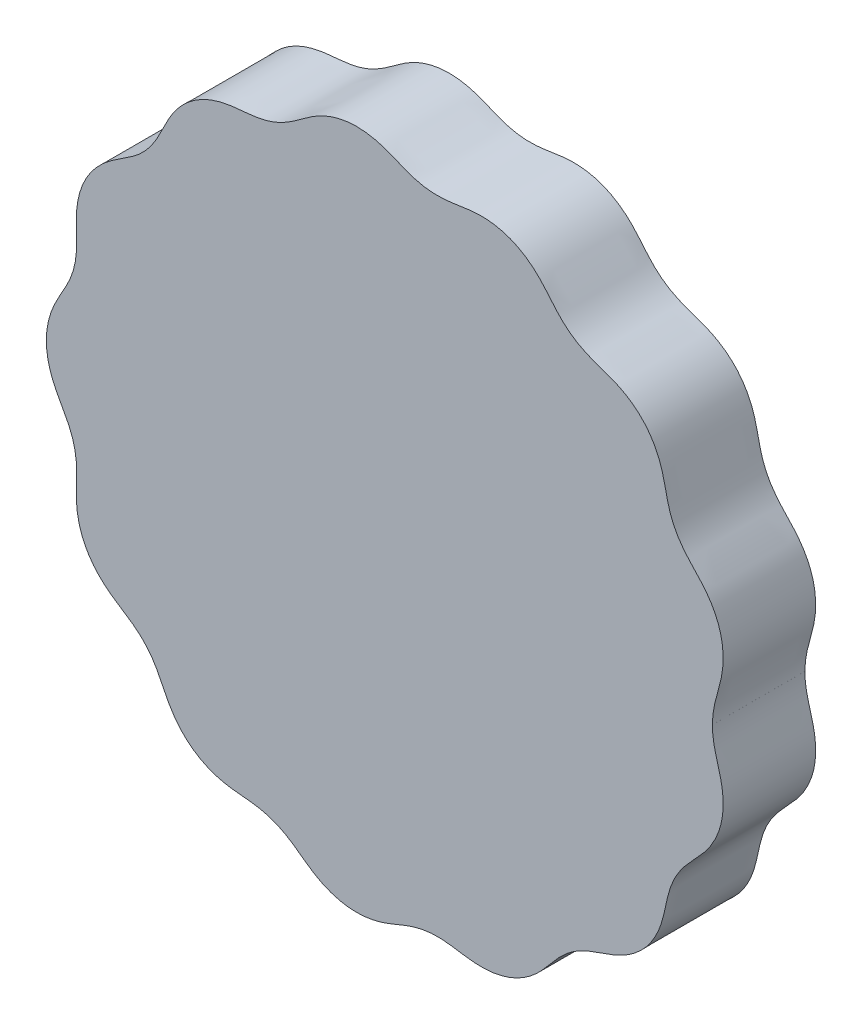
SolidWorks part; units mm, degrees
ref_plane "Front Plane" through (0, 0, 0) normal (0, 0, 1) x (1, 0, 0)
ref_plane "Top Plane" through (0, 0, 0) normal (0, 1, 0) x (1, 0, 0)
ref_plane "Right Plane" through (0, 0, 0) normal (1, 0, 0) x (0, 0, -1)
sketch "Sketch1" plane through (0, 0, 0) normal (0, 0, 1) x (1, 0, 0)
  spline S0 degree 4 poles (29.7584, 20.3385) (29.7891, 20.21) (29.8482, 19.9526) (29.9598, 19.4358) (30.1239, 18.6606) (30.3526, 17.7631) (30.7964, 16.5535) (31.4244, 15.4416) (32.2108, 14.4638) (33.1915, 13.4281) (34.1349, 12.4283) (35.0241, 11.2132) (35.7198, 9.7379) (36.1228, 8.1778) (36.2154, 6.7983) (36.1087, 5.5837) (35.9167, 4.6243) (35.7472, 3.9584) (35.5841, 3.3729) (35.4416, 2.864) (35.3243, 2.4166) (35.2341, 2.0306) (35.1681, 1.7068) (35.1214, 1.4469) (35.0816, 1.1852) (35.0491, 0.9241) (35.0274, 0.6907) (35.0151, 0.515) (35.0085, 0.3814) (35.0032, 0.2408) (34.9995, 0.0558) (34.9993, -0.0463) (35.0036, -0.2609) (35.011, -0.4439) (35.0217, -0.6152) (35.0388, -0.8202) (35.0646, -1.0542) (35.1044, -1.3447) (35.1634, -1.6922) (35.2469, -2.0945) (35.3584, -2.5508) (35.4807, -3.0042) (35.6346, -3.553) (35.8127, -4.1993) (35.9906, -4.9498) (36.1279, -5.8113) (36.1828, -6.6338) (36.163, -7.4097) (36.0619, -8.3015) (35.8756, -9.1315) (35.6003, -9.9363) (35.2413, -10.706) (34.9069, -11.2975) (34.4713, -11.9491) (33.919, -12.6455) (33.2464, -13.3753) (32.4862, -14.1654) (31.7296, -15.0492) (31.0461, -16.0739) (30.5313, -17.1947) (30.1828, -18.3744) (29.944, -19.5117) (29.7144, -20.5842) (29.2958, -22.0281) (28.4622, -23.7586) (27.0395, -25.4117) (25.2208, -26.5522) (23.6326, -27.1562) (22.3082, -27.5963) (21.1226, -28.0489) (19.9984, -28.666) (18.9904, -29.4694) (18.1793, -30.3103) (17.5068, -31.117) (16.775, -32.0038) (15.9108, -32.911) (14.604, -33.9568) (12.974, -34.7587) (11.1723, -35.1688) (9.4524, -35.1689) (8.1807, -35.0073) (7.0608, -34.8246) (6.0778, -34.7001) (4.9253, -34.6549) (3.6117, -34.7857) (2.349, -35.145) (1.1515, -35.6432) (0.1111, -36.0773) (-0.7914, -36.3968) (-2.1459, -36.7469) (-3.9895, -36.8999) (-5.8676, -36.5696) (-7.6084, -35.7603) (-8.8563, -34.9233) (-9.733, -34.2648) (-10.6766, -33.5857) (-11.7416, -32.9684) (-12.8897, -32.517) (-14.0912, -32.248) (-15.2466, -32.1165) (-16.3395, -32.0314) (-17.4939, -31.8907) (-18.6927, -31.6153) (-20.2224, -31.0274) (-21.7615, -30.0159) (-23.1071, -28.5705) (-24.107, -26.7907) (-24.8246, -25.168) (-25.6288, -23.8316) (-26.5069, -22.8288) (-27.3779, -22.0818) (-28.1653, -21.5233) (-29.1173, -20.9169) (-30.1989, -20.207) (-31.2694, -19.3076) (-32.2317, -18.16) (-32.9494, -16.9232) (-33.4333, -15.6485) (-33.6955, -14.3778) (-33.7784, -13.1508) (-33.7526, -11.9888) (-33.7086, -10.893) (-33.7328, -9.7296) (-33.9076, -8.5101) (-34.2723, -7.3318) (-34.7987, -6.2202) (-35.3756, -5.2116) (-35.913, -4.2559) (-36.5515, -2.8948) (-37.0651, -1.0442) (-37.082, 0.8932) (-36.604, 2.7435) (-35.9923, 4.1013) (-35.4727, 5.0451) (-34.8935, 6.0468) (-34.342, 7.1566) (-33.946, 8.3403) (-33.7454, 9.5758) (-33.7062, 10.7488) (-33.746, 11.8447) (-33.7797, 13.0063) (-33.7137, 14.234) (-33.4725, 15.5088) (-33.0106, 16.7916) (-32.323, 18.0254) (-31.4056, 19.1641) (-30.3765, 20.071) (-29.3206, 20.7894) (-28.3591, 21.3964) (-27.534, 21.9617) (-26.6421, 22.6971) (-25.7533, 23.6668) (-25.0522, 24.7709) (-24.489, 25.9341) (-23.9968, 26.9508) (-23.5268, 27.7958) (-22.7368, 28.9589) (-21.4481, 30.2928) (-19.8158, 31.2833) (-17.9732, 31.822) (-16.4836, 32.0177) (-15.3906, 32.1053) (-14.2341, 32.2258) (-13.0286, 32.476) (-11.8723, 32.9062) (-10.7976, 33.5073) (-9.8477, 34.1778) (-8.9731, 34.8386) (-8.0137, 35.4955) (-6.9309, 36.0792) (-5.393, 36.6451) (-3.5734, 36.898) (-1.6184, 36.6998) (0.3038, 36.0279) (1.9171, 35.2896) (3.4089, 34.8257) (4.7366, 34.663) (5.8813, 34.6859) (6.8315, 34.7908) (7.9438, 34.968) (9.229, 35.1535) (10.6343, 35.1866) (12.124, 34.9573) (13.489, 34.4966) (14.703, 33.8498) (15.7429, 33.0588) (16.6157, 32.1841) (17.5363, 31.0896) (18.4486, 29.9665) (19.5936, 28.9216) (20.9289, 28.1422) (22.1052, 27.6653) (23.222, 27.294) (24.2457, 26.9278) (25.6089, 26.3102) (27.1929, 25.2322) (28.4595, 23.7628) (29.2939, 22.0329) (29.7133, 20.589) (29.943, 19.5166) (30.1817, 18.3793) (30.5296, 17.1994) (31.0437, 16.0783) (31.7265, 15.0531) (32.4828, 14.1691) (33.2429, 13.3788) (34.0308, 12.5245) (34.7785, 11.548) (35.3354, 10.5681) (35.7176, 9.6216) (35.9489, 8.8043) (36.0802, 8.1376) (36.1627, 7.4147) (36.1829, 6.6388) (36.1284, 5.8162) (35.9916, 4.9547) (35.7869, 4.0898) (35.5719, 3.332) (35.3876, 2.6696) (35.2481, 2.0994) (35.1523, 1.6394) (35.0863, 1.234) (35.0442, 0.884) (35.022, 0.6202) (35.0113, 0.4489) (35.0037, 0.2659) (34.9993, 0.0512) (34.9994, -0.0508) (35.0031, -0.2358) (35.0082, -0.3765) (35.0147, -0.51) (35.027, -0.6858) (35.0485, -0.9192) (35.0809, -1.1803) (35.1206, -1.442) (35.1671, -1.702) (35.2331, -2.0258) (35.3231, -2.4118) (35.4403, -2.8592) (35.5827, -3.3682) (35.746, -3.9537) (35.9156, -4.6195) (36.108, -5.5789) (36.2154, -6.7934) (36.1235, -8.173) (35.7214, -9.7334) (35.0265, -11.2091) (34.1379, -12.4247) (33.1948, -13.4247) (32.2139, -14.4604) (31.427, -15.4378) (30.7984, -16.5494) (30.3539, -17.7588) (30.1249, -18.6563) (29.9607, -19.4314) (29.8492, -19.9482) (29.7901, -20.2057) (29.7594, -20.3342) knots 0 0 0 0 0 0.001898 0.003795 0.007591 0.011386 0.015182 0.022267 0.02581 0.029353 0.035677 0.042002 0.047317 0.052632 0.058704 0.06174 0.064776 0.066674 0.068572 0.070469 0.072367 0.073316 0.074265 0.075214 0.076163 0.077112 0.078061 0.078535 0.078772 0.07901 0.079959 0.080802 0.081223 0.081645 0.082488 0.083331 0.084174 0.085017 0.086703 0.08839 0.090076 0.091762 0.093448 0.096577 0.099706 0.102834 0.105963 0.1084 0.110837 0.115712 0.118149 0.120587 0.123024 0.125461 0.129399 0.133337 0.137274 0.141212 0.14609 0.150967 0.154905 0.158843 0.162781 0.166719 0.176468 0.186218 0.193523 0.197175 0.200827 0.206276 0.211725 0.215495 0.219265 0.223035 0.226805 0.232015 0.237225 0.246974 0.252616 0.258259 0.261813 0.265368 0.268922 0.272477 0.278357 0.284237 0.287673 0.291109 0.294545 0.297981 0.307731 0.317479 0.321417 0.325355 0.329292 0.33323 0.338109 0.342987 0.346925 0.350862 0.3548 0.358737 0.363612 0.368487 0.378236 0.384925 0.391614 0.397677 0.403741 0.407204 0.410667 0.414131 0.417594 0.423418 0.429243 0.434118 0.438993 0.443867 0.448741 0.452679 0.456618 0.460556 0.464494 0.469373 0.474251 0.478188 0.482125 0.486061 0.489998 0.499749 0.509498 0.513366 0.517234 0.521101 0.524969 0.529987 0.535005 0.538943 0.542881 0.546818 0.550756 0.555631 0.560505 0.56538 0.570255 0.575829 0.581404 0.584992 0.58858 0.592168 0.595756 0.60157 0.607383 0.610853 0.614322 0.617791 0.621261 0.631011 0.64076 0.644697 0.648635 0.652573 0.65651 0.66139 0.66627 0.670207 0.674144 0.678081 0.682018 0.686892 0.691767 0.701517 0.708138 0.71476 0.72089 0.72702 0.73045 0.733879 0.737309 0.740738 0.74663 0.752523 0.757398 0.762273 0.767233 0.772192 0.776088 0.779983 0.787773 0.792971 0.798169 0.802072 0.805975 0.809877 0.81378 0.82353 0.833279 0.837217 0.841155 0.845093 0.849031 0.853908 0.858786 0.862724 0.866661 0.870599 0.874537 0.879411 0.884286 0.886723 0.889161 0.891598 0.894035 0.897164 0.900292 0.903421 0.90655 0.909922 0.911608 0.913295 0.914981 0.916667 0.91751 0.918353 0.918775 0.919196 0.920039 0.920988 0.921226 0.921463 0.921937 0.922886 0.923835 0.924784 0.925733 0.926682 0.927631 0.929529 0.931427 0.933325 0.935222 0.938259 0.941295 0.947367 0.952682 0.957997 0.964322 0.970647 0.97419 0.977732 0.984818 0.988613 0.992409 0.996204 0.998102 1 1 1 1 1 construction
  spline S1 degree 4 poles (35, 0) (35, -0.0493) (35.0008, -0.1235) (35.0036, -0.2609) (35.011, -0.4439) (35.0217, -0.6152) (35.0388, -0.8202) (35.0646, -1.0542) (35.1044, -1.3447) (35.1634, -1.6922) (35.2469, -2.0945) (35.3584, -2.5508) (35.4807, -3.0042) (35.6346, -3.553) (35.8127, -4.1993) (35.9906, -4.9498) (36.1279, -5.8113) (36.1828, -6.6338) (36.163, -7.4097) (36.0619, -8.3015) (35.8756, -9.1315) (35.6003, -9.9363) (35.2413, -10.706) (34.9069, -11.2975) (34.4713, -11.9491) (33.919, -12.6455) (33.2464, -13.3753) (32.4862, -14.1654) (31.7296, -15.0492) (31.0461, -16.0739) (30.5313, -17.1947) (30.1828, -18.3744) (29.944, -19.5117) (29.7144, -20.5842) (29.2958, -22.0281) (28.4622, -23.7586) (27.0395, -25.4117) (25.2208, -26.5522) (23.6326, -27.1562) (22.3082, -27.5963) (21.1226, -28.0489) (19.9984, -28.666) (18.9904, -29.4694) (18.1793, -30.3103) (17.5068, -31.117) (16.775, -32.0038) (15.9108, -32.911) (14.604, -33.9568) (12.974, -34.7587) (11.1723, -35.1688) (9.4524, -35.1689) (8.1807, -35.0073) (7.0608, -34.8246) (6.0778, -34.7001) (4.9253, -34.6549) (3.6117, -34.7857) (2.349, -35.145) (1.1515, -35.6432) (0.1111, -36.0773) (-0.7914, -36.3968) (-2.1459, -36.7469) (-3.9895, -36.8999) (-5.8676, -36.5696) (-7.6084, -35.7603) (-8.8563, -34.9233) (-9.733, -34.2648) (-10.6766, -33.5857) (-11.7416, -32.9684) (-12.8897, -32.517) (-14.0912, -32.248) (-15.2466, -32.1165) (-16.3395, -32.0314) (-17.4939, -31.8907) (-18.6927, -31.6153) (-20.2224, -31.0274) (-21.7615, -30.0159) (-23.1071, -28.5705) (-24.107, -26.7907) (-24.8246, -25.168) (-25.6288, -23.8316) (-26.5069, -22.8288) (-27.3779, -22.0818) (-28.1653, -21.5233) (-29.1173, -20.9169) (-30.1989, -20.207) (-31.2694, -19.3076) (-32.2317, -18.16) (-32.9494, -16.9232) (-33.4333, -15.6485) (-33.6955, -14.3778) (-33.7784, -13.1508) (-33.7526, -11.9888) (-33.7086, -10.893) (-33.7328, -9.7296) (-33.9076, -8.5101) (-34.2723, -7.3318) (-34.7987, -6.2202) (-35.3756, -5.2116) (-35.913, -4.2559) (-36.5515, -2.8948) (-37.0651, -1.0442) (-37.082, 0.8932) (-36.604, 2.7435) (-35.9923, 4.1013) (-35.4727, 5.0451) (-34.8935, 6.0468) (-34.342, 7.1566) (-33.946, 8.3403) (-33.7454, 9.5758) (-33.7062, 10.7488) (-33.746, 11.8447) (-33.7797, 13.0063) (-33.7137, 14.234) (-33.4725, 15.5088) (-33.0106, 16.7916) (-32.323, 18.0254) (-31.4056, 19.1641) (-30.3765, 20.071) (-29.3206, 20.7894) (-28.3591, 21.3964) (-27.534, 21.9617) (-26.6421, 22.6971) (-25.7533, 23.6668) (-25.0522, 24.7709) (-24.489, 25.9341) (-23.9968, 26.9508) (-23.5268, 27.7958) (-22.7368, 28.9589) (-21.4481, 30.2928) (-19.8158, 31.2833) (-17.9732, 31.822) (-16.4836, 32.0177) (-15.3906, 32.1053) (-14.2341, 32.2258) (-13.0286, 32.476) (-11.8723, 32.9062) (-10.7976, 33.5073) (-9.8477, 34.1778) (-8.9731, 34.8386) (-8.0137, 35.4955) (-6.9309, 36.0792) (-5.393, 36.6451) (-3.5734, 36.898) (-1.6184, 36.6998) (0.3038, 36.0279) (1.9171, 35.2896) (3.4089, 34.8257) (4.7366, 34.663) (5.8813, 34.6859) (6.8315, 34.7908) (7.9438, 34.968) (9.229, 35.1535) (10.6343, 35.1866) (12.124, 34.9573) (13.489, 34.4966) (14.703, 33.8498) (15.7429, 33.0588) (16.6157, 32.1841) (17.5363, 31.0896) (18.4486, 29.9665) (19.5936, 28.9216) (20.9289, 28.1422) (22.1052, 27.6653) (23.222, 27.294) (24.2457, 26.9278) (25.6089, 26.3102) (27.1929, 25.2322) (28.4595, 23.7628) (29.2939, 22.0329) (29.7133, 20.589) (29.943, 19.5166) (30.1817, 18.3793) (30.5296, 17.1994) (31.0437, 16.0783) (31.7265, 15.0531) (32.4828, 14.1691) (33.2429, 13.3788) (34.0308, 12.5245) (34.7785, 11.548) (35.3354, 10.5681) (35.7176, 9.6216) (35.9489, 8.8043) (36.0802, 8.1376) (36.1627, 7.4147) (36.1829, 6.6388) (36.1284, 5.8162) (35.9916, 4.9547) (35.7869, 4.0898) (35.5719, 3.332) (35.3876, 2.6696) (35.2481, 2.0994) (35.1523, 1.6394) (35.0863, 1.234) (35.0442, 0.884) (35.022, 0.6202) (35.0113, 0.4489) (35.0037, 0.2659) (35.0009, 0.1285) (35, 0.0543) (35, 0.005) knots 0.079959 0.079959 0.079959 0.079959 0.079959 0.080802 0.081223 0.081645 0.082488 0.083331 0.084174 0.085017 0.086703 0.08839 0.090076 0.091762 0.093448 0.096577 0.099706 0.102834 0.105963 0.1084 0.110837 0.115712 0.118149 0.120587 0.123024 0.125461 0.129399 0.133337 0.137274 0.141212 0.14609 0.150967 0.154905 0.158843 0.162781 0.166719 0.176468 0.186218 0.193523 0.197175 0.200827 0.206276 0.211725 0.215495 0.219265 0.223035 0.226805 0.232015 0.237225 0.246974 0.252616 0.258259 0.261813 0.265368 0.268922 0.272477 0.278357 0.284237 0.287673 0.291109 0.294545 0.297981 0.307731 0.317479 0.321417 0.325355 0.329292 0.33323 0.338109 0.342987 0.346925 0.350862 0.3548 0.358737 0.363612 0.368487 0.378236 0.384925 0.391614 0.397677 0.403741 0.407204 0.410667 0.414131 0.417594 0.423418 0.429243 0.434118 0.438993 0.443867 0.448741 0.452679 0.456618 0.460556 0.464494 0.469373 0.474251 0.478188 0.482125 0.486061 0.489998 0.499749 0.509498 0.513366 0.517234 0.521101 0.524969 0.529987 0.535005 0.538943 0.542881 0.546818 0.550756 0.555631 0.560505 0.56538 0.570255 0.575829 0.581404 0.584992 0.58858 0.592168 0.595756 0.60157 0.607383 0.610853 0.614322 0.617791 0.621261 0.631011 0.64076 0.644697 0.648635 0.652573 0.65651 0.66139 0.66627 0.670207 0.674144 0.678081 0.682018 0.686892 0.691767 0.701517 0.708138 0.71476 0.72089 0.72702 0.73045 0.733879 0.737309 0.740738 0.74663 0.752523 0.757398 0.762273 0.767233 0.772192 0.776088 0.779983 0.787773 0.792971 0.798169 0.802072 0.805975 0.809877 0.81378 0.82353 0.833279 0.837217 0.841155 0.845093 0.849031 0.853908 0.858786 0.862724 0.866661 0.870599 0.874537 0.879411 0.884286 0.886723 0.889161 0.891598 0.894035 0.897164 0.900292 0.903421 0.90655 0.909922 0.911608 0.913295 0.914981 0.916667 0.91751 0.918353 0.918775 0.919196 0.920039 0.920039 0.920039 0.920039 0.920039
  spline S2 degree 1 poles (35, 0.005) (35, 0) knots 0 0 1 1
extrude "Boss-Extrude1" add sketch "Sketch1" along normal blind 10
